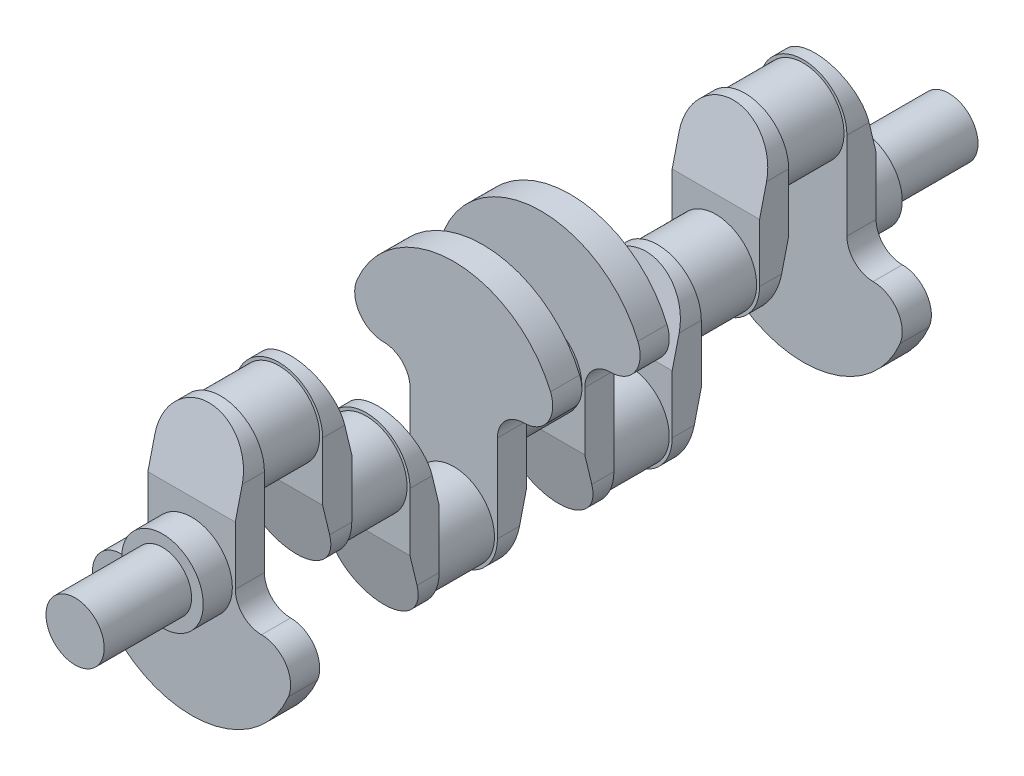
SolidWorks part; units mm, degrees
ref_plane "Front Plane" through (0, 0, 0) normal (0, 0, 1) x (1, 0, 0)
ref_plane "Top Plane" through (0, 0, 0) normal (0, 1, 0) x (1, 0, 0)
ref_plane "Right Plane" through (0, 0, 0) normal (1, 0, 0) x (0, 0, -1)
sketch "Sketch1" plane through (0, 0, 0) normal (0, 0, 1) x (1, 0, 0)
  line L0 (0, 215.8882) -> (0, -268.1509) construction
  line L3 (-75, 120) -> (-75, -30)
  line L4 (75, 120) -> (75, -30)
  arc A10 (-75, -30) -> (-120, -75) centre (-120, -30) cw
  arc A11 (-120, -75) -> (-166.1538, -144.2308) centre (-120, -125) ccw
  arc A12 (120, -75) -> (166.1538, -144.2308) centre (120, -125) cw
  arc A13 (75, -30) -> (120, -75) centre (120, -30) ccw
  arc A14 (-75, 120) -> (75, 120) centre (0, 120) cw
  arc A15 (-166.1538, -144.2308) -> (166.1538, -144.2308) centre (0, -75) ccw
  point P19 (0, 195)
  point P20 (0, -255)
  dimension "D2" = 75
  dimension "D3" = 180
  dimension "D4" = 45
  dimension "D5" = 50
  dimension "D6" = 75
  dimension "D1" = 150
  dimension "D7" = 450
extrude "Boss-Extrude1" add sketch "Sketch1" along normal blind 50
sketch "Sketch5" plane through (75, 0, 0) normal (1, 0, 0) x (0, 0, -1)
  line L0 (-50, 70) -> (-50, 195)
  line L1 (-50, -30) -> (-50, 120) construction
  line L2 (-50, 195) -> (-20, 195)
  line L3 (0, 195) -> (-50, 195) construction
  line L4 (-20, 195) -> (-50, 70)
  dimension "D1" = 125
  dimension "D2" = 30
extrude "Cut-Extrude1" cut sketch "Sketch5" against normal through all
sketch "Sketch6" plane through (0, 0, 0) normal (0, 0, -1) x (-1, 0, 0)
  circle A0 centre (0, 120) radius 70
  arc A1 (75, 120) -> (-75, 120) centre (0, 120) ccw construction
  dimension "D1" = 140
extrude "Boss-Extrude2" add sketch "Sketch6" along normal blind 100
sketch "Sketch7" plane through (0, 0, -100) normal (0, 0, -1) x (-1, 0, 0)
  line L0 (0, 120) -> (0, -30) construction
  line L1 (75, 120) -> (75, -30)
  line L2 (-75, 120) -> (-75, -30)
  arc A0 (75, 120) -> (-75, 120) centre (0, 120) ccw
  arc A1 (-75, -30) -> (75, -30) centre (0, -30) ccw
  point P4 (0, 45)
  dimension "D2" = 75
  dimension "D1" = 150
extrude "Boss-Extrude3" add sketch "Sketch7" along normal blind 50
sketch "Sketch8" plane through (0, 0, -150) normal (0, 0, -1) x (-1, 0, 0)
  circle A0 centre (0, -30) radius 70
  arc A1 (-75, -30) -> (75, -30) centre (0, -30) ccw construction
  dimension "D1" = 140
extrude "Boss-Extrude4" add sketch "Sketch8" along normal blind 100
sketch "Sketch9" plane through (0, 0, -250) normal (0, 0, -1) x (-1, 0, 0)
  line L0 (0, -30) -> (0, -180) construction
  line L1 (75, -30) -> (75, -180)
  line L2 (-75, -30) -> (-75, -180)
  arc A0 (75, -30) -> (-75, -30) centre (0, -30) ccw
  arc A1 (-75, -180) -> (75, -180) centre (0, -180) ccw
  point P4 (0, -105)
  dimension "D2" = 75
  dimension "D1" = 150
extrude "Boss-Extrude5" add sketch "Sketch9" along normal blind 50
sketch "Sketch10" plane through (0, 0, -300) normal (0, 0, -1) x (-1, 0, 0)
  circle A0 centre (0, -180) radius 70
  arc A1 (-75, -180) -> (75, -180) centre (0, -180) ccw construction
  dimension "D1" = 140
extrude "Boss-Extrude6" add sketch "Sketch10" along normal blind 100
sketch "Sketch11" plane through (0, 0, -400) normal (0, 0, -1) x (-1, 0, 0)
  line L0 (-120, -30) -> (-120, -125) construction
  line L1 (120, -30) -> (-120, -30) construction
  line L4 (75, -180) -> (75, -30)
  line L5 (-75, -30) -> (-75, -180)
  line L6 (0, 120) -> (0, -180) construction
  arc A12 (120, 15) -> (75, -30) centre (120, -30) ccw
  arc A13 (120, 15) -> (166.1538, 84.2308) centre (120, 65) ccw
  arc A14 (166.1538, 84.2308) -> (-166.1538, 84.2308) centre (0, 15) ccw
  arc A15 (-166.1538, 84.2308) -> (-120, 15) centre (-120, 65) ccw
  arc A16 (-75, -30) -> (-120, 15) centre (-120, -30) ccw
  arc A17 (-75, -180) -> (75, -180) centre (0, -180) ccw
  point P2 (0, -30)
  point P8 (0, 195)
  dimension "D2" = 225
extrude "Boss-Extrude7" add sketch "Sketch11" along normal blind 50
sketch "Sketch12" plane through (0, 0, -450) normal (0, 0, -1) x (-1, 0, 0)
  circle A0 centre (0, -30) radius 70
  point P2 (0, 0)
  point P4 (0, 0)
  dimension "D1" = 140
  dimension "D2" = 30
extrude "Boss-Extrude8" add sketch "Sketch12" along normal blind 50 contours A0
sketch "Sketch13" plane through (0, 0, 50) normal (0, 0, 1) x (1, 0, 0)
  circle A1 centre (0, -30) radius 70
  circle A2 centre (0, -30) radius 70
  dimension "D1" = 0
extrude "Boss-Extrude9" add sketch "Sketch13" along normal blind 50
sketch "Sketch14" plane through (0, 0, 100) normal (0, 0, 1) x (1, 0, 0)
  circle A0 centre (0, -30) radius 50
  dimension "D1" = 100
extrude "Boss-Extrude11" add sketch "Sketch14" along normal blind 150
sketch "Sketch15" plane through (75, 0, 0) normal (1, 0, 0) x (0, 0, -1)
  line L0 (100, 20) -> (100, -105)
  line L1 (100, 120) -> (100, -30) construction
  line L2 (100, -105) -> (130, -105)
  line L3 (100, -105) -> (150, -105) construction
  line L4 (130, -105) -> (100, 20)
  line L5 (150, 70) -> (150, 195)
  line L6 (150, 120) -> (150, -30) construction
  line L7 (150, 195) -> (120, 195)
  line L8 (150, 195) -> (100, 195) construction
  line L9 (120, 195) -> (150, 70)
  line L10 (300, -80) -> (300, 45)
  line L11 (300, -30) -> (300, -180) construction
  line L12 (300, -30) -> (300, 45) construction
  line L13 (300, 45) -> (270, 45)
  line L14 (300, 45) -> (250, 45) construction
  line L15 (270, 45) -> (300, -80)
  line L16 (250, -130) -> (250, -255)
  line L17 (250, -30) -> (250, -180) construction
  line L18 (250, -255) -> (280, -255)
  line L20 (280, -255) -> (250, -130)
  line L21 (450, -130) -> (450, -255)
  line L22 (450, -30) -> (450, -180) construction
  line L23 (450, -255) -> (420, -255)
  line L24 (400, -255) -> (450, -255) construction
  line L25 (420, -255) -> (450, -130)
  point P32 (0, 0)
  point P38 (0, 0)
  point P42 (0, 0)
  dimension "D1" = 125
  dimension "D2" = 30
  dimension "D3" = 30
  dimension "D4" = 125
  dimension "D5" = 125
  dimension "D6" = 125
  dimension "D7" = 30
  dimension "D8" = 30
  dimension "D9" = 125
  dimension "D10" = 30
extrude "Cut-Extrude2" cut sketch "Sketch15" against normal through all
mirror "Mirror2" about plane through (0, -30, -500) normal (0, 0, -1) of bodies 113
